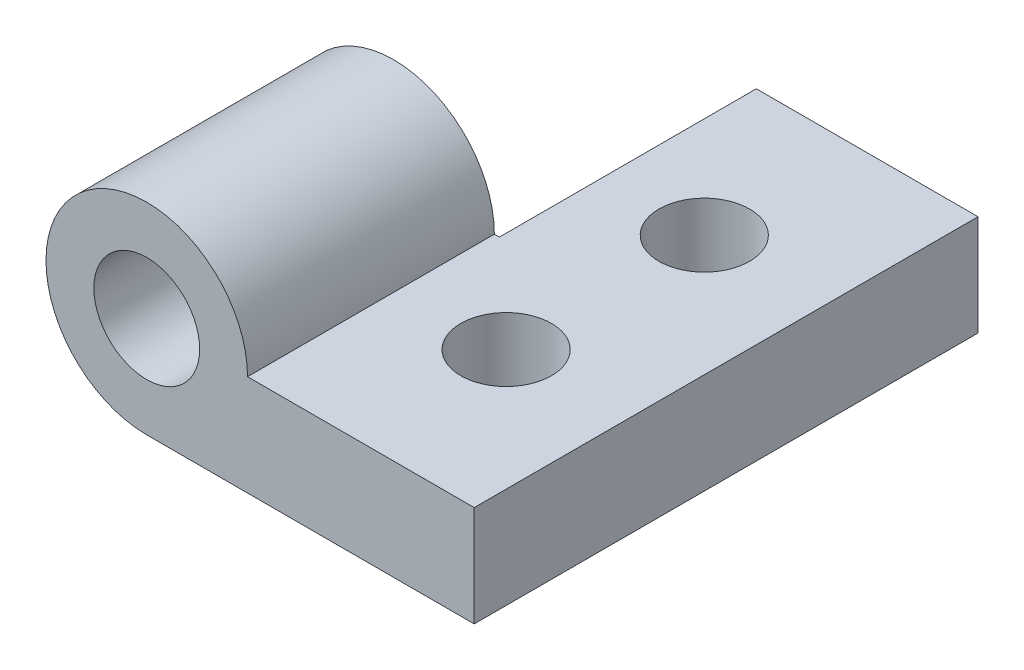
SolidWorks part; units mm, degrees
ref_plane "Front Plane" through (0, 0, 0) normal (0, 0, 1) x (1, 0, 0)
ref_plane "Top Plane" through (0, 0, 0) normal (0, 1, 0) x (1, 0, 0)
ref_plane "Right Plane" through (0, 0, 0) normal (1, 0, 0) x (0, 0, -1)
sketch "Sketch2" plane through (0, 0, 0) normal (0, 0, 1) x (1, 0, 0)
  line L1 (0, 0) -> (-16.51, 0)
  line L2 (0, 0) -> (0, 5.08)
  line L3 (0, 5.08) -> (-11.43, 5.08)
  arc A0 (-11.43, 5.08) -> (-16.51, 0) centre (-16.51, 5.08) ccw
  dimension "D3" = 5.08
  dimension "D1" = 16.51
  dimension "D2" = 5.08
extrude "Boss-Extrude1" add sketch "Sketch2" along normal blind 25.4
sketch "Sketch5" plane through (0, 5.08, 0) normal (0, 1, 0) x (1, 0, 0)
  line L0 (-6.096, -15.4093) -> (-6.096, -9.9907) construction
  line L1 (-6.096, -19.9813) -> (-6.096, -25.4) construction
  line L2 (0, -25.4) -> (-11.43, -25.4) construction
  line L3 (-6.096, -5.4187) -> (-6.096, 0) construction
  line L4 (0, 0) -> (-11.43, 0) construction
  line L5 (-6.096, -7.7047) -> (-16.51, -7.7047) construction
  line L9 (-16.51, -25.4) -> (-16.51, 0) construction
  circle A0 centre (-6.096, -17.6953) radius 2.286
  circle A1 centre (-6.096, -7.7047) radius 2.286
  dimension "D1" = 4.572
  dimension "D2" = 4.572
  dimension "D3" = 10.414
extrude "Cut-Extrude3" cut sketch "Sketch5" against normal blind 12.954
sketch "Sketch8" plane through (0, 0, 0) normal (0, 0, -1) x (-1, 0, 0)
  circle A0 centre (19.3527, 9.2811) radius 0.0075
  circle A1 centre (16.51, 5.08) radius 5.08
  circle A2 centre (16.51, 5.08) radius 5.334
  dimension "D1" = 10.668
extrude "Cut-Extrude5" cut sketch "Sketch8" against normal blind 12.954 contours A2
sketch "Sketch9" plane through (0, 0, 12.954) normal (0, 0, -1) x (-1, 0, 0)
  circle A0 centre (16.51, 5.08) radius 5.08
  circle A1 centre (16.51, 5.08) radius 2.667
  dimension "D1" = 5.334
extrude "Cut-Extrude6" cut sketch "Sketch9" against normal blind 12.7 contours A1
